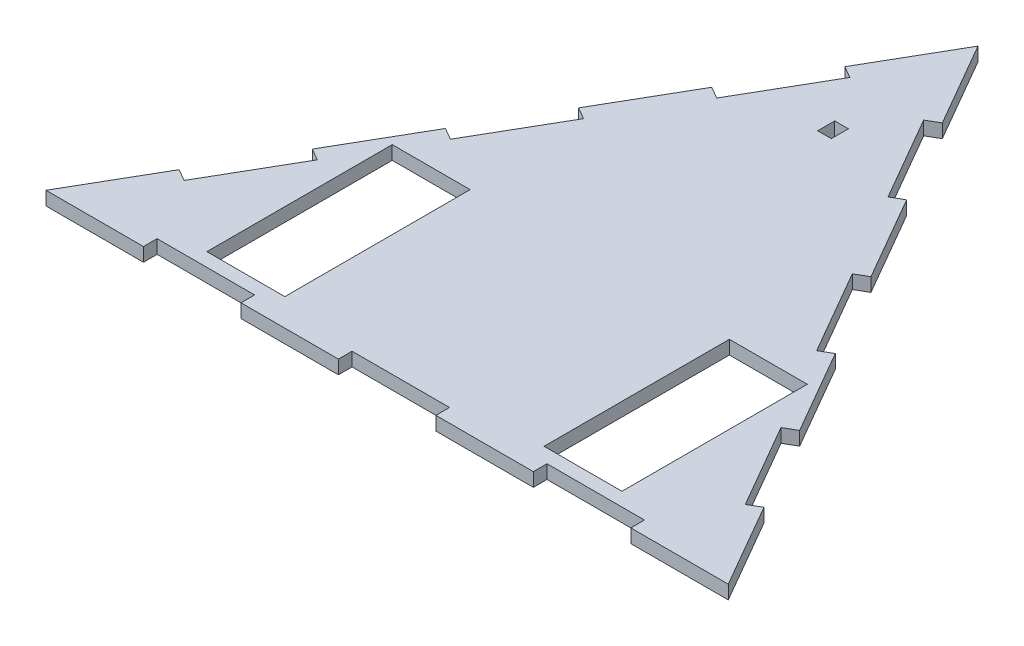
SolidWorks part; units mm, degrees
ref_plane "Front Plane" through (0, 0, 0) normal (0, 0, 1) x (1, 0, 0)
ref_plane "Top Plane" through (0, 0, 0) normal (0, 1, 0) x (1, 0, 0)
ref_plane "Right Plane" through (0, 0, 0) normal (1, 0, 0) x (0, 0, -1)
sketch "Sketch1" plane through (0, 0, 0) normal (0, 1, 0) x (1, 0, 0)
  line L0 (0, 0) -> (-254, 0)
  line L1 (-254, 0) -> (-127, 219.9705)
  line L2 (-127, 219.9705) -> (0, 0)
  dimension "D1" = 254
  dimension "D2" = 254
  dimension "D3" = 254
extrude "Boss-Extrude1" add sketch "Sketch1" along normal blind 5.08
sketch "Sketch4" plane through (0, 5.08, 0) normal (0, 1, 0) x (1, 0, 0)
  line L0 (-127, 0) -> (-175.26, 0) construction
  line L1 (-254, 0) -> (0, 0) construction
  line L2 (-127, 0) -> (-78.74, 0) construction
  line L3 (-175.26, 0) -> (-175.26, 10.16)
  line L4 (-78.74, 0) -> (-78.74, 10.16)
  line L6 (-175.26, 10.16) -> (-204.26, 10.16)
  line L7 (-175.26, 10.16) -> (-175.26, 79.16)
  line L8 (-175.26, 79.16) -> (-204.26, 79.16)
  line L9 (-204.26, 10.16) -> (-204.26, 79.16)
  line L10 (-78.74, 10.16) -> (-49.74, 10.16)
  line L11 (-78.74, 10.16) -> (-78.74, 79.16)
  line L12 (-78.74, 79.16) -> (-49.74, 79.16)
  line L13 (-49.74, 10.16) -> (-49.74, 79.16)
  dimension "D1" = 48.26
  dimension "D2" = 48.26
  dimension "D3" = 10.16
  dimension "D4" = 10.16
  dimension "D5" = 69
  dimension "D6" = 29
  dimension "D7" = 69
  dimension "D8" = 29
extrude "Cut-Extrude1" cut sketch "Sketch4" against normal blind 5.08 contours L9 L6 L7 L8 | L10 L13 L12 L11
sketch "Sketch8" plane through (-190.5, 0, -109.9852) normal (-0.866, 0, -0.5) x (-0.5, 0, 0.866)
  line L0 (-127, 0) -> (-90.7143, 0) construction
  line L1 (-127, 0) -> (127, 0) construction
  line L2 (-90.7143, 0) -> (-54.4286, 0) construction
  line L3 (-54.4286, 0) -> (-18.1429, 0) construction
  line L4 (-18.1429, 0) -> (18.1429, 0) construction
  line L5 (18.1429, 0) -> (54.4286, 0) construction
  line L6 (54.4286, 0) -> (90.7143, 0) construction
  line L7 (90.7143, 0) -> (127, 0) construction
  line L8 (-127, 5.08) -> (127, 5.08) construction
  line L9 (-90.7143, 0) -> (-54.4286, 0)
  line L10 (-90.7143, 0) -> (-90.7143, 5.08)
  line L11 (-90.7143, 5.08) -> (-54.4286, 5.08)
  line L12 (-54.4286, 0) -> (-54.4286, 5.08)
  line L14 (-18.1429, 0) -> (18.1429, 0)
  line L15 (-18.1429, 0) -> (-18.1429, 5.08)
  line L16 (-18.1429, 5.08) -> (18.1429, 5.08)
  line L17 (18.1429, 0) -> (18.1429, 5.08)
  line L18 (54.4286, 0) -> (90.7143, 0)
  line L19 (54.4286, 0) -> (54.4286, 5.08)
  line L20 (54.4286, 5.08) -> (90.7143, 5.08)
  line L21 (90.7143, 0) -> (90.7143, 5.08)
extrude "Cut-Extrude2" cut sketch "Sketch8" against normal blind 5.08
sketch "Sketch9" plane through (0, 0, 0) normal (0, 0, 1) x (1, 0, 0)
  line L0 (0, 0) -> (-36.2857, 0) construction
  line L1 (-254, 0) -> (0, 0) construction
  line L2 (-36.2857, 0) -> (-72.5714, 0) construction
  line L3 (-72.5714, 0) -> (-108.8571, 0) construction
  line L4 (-108.8571, 0) -> (-145.1429, 0) construction
  line L5 (-145.1429, 0) -> (-181.4286, 0) construction
  line L6 (-181.4286, 0) -> (-217.7143, 0) construction
  line L7 (-217.7143, 0) -> (-254, 0) construction
  line L8 (-254, 5.08) -> (0, 5.08) construction
  line L9 (-36.2857, 0) -> (-72.5714, 0)
  line L10 (-36.2857, 0) -> (-36.2857, 5.08)
  line L11 (-36.2857, 5.08) -> (-72.5714, 5.08)
  line L12 (-72.5714, 0) -> (-72.5714, 5.08)
  line L14 (-108.8571, 0) -> (-145.1429, 0)
  line L15 (-108.8571, 0) -> (-108.8571, 5.08)
  line L16 (-108.8571, 5.08) -> (-145.1429, 5.08)
  line L17 (-145.1429, 0) -> (-145.1429, 5.08)
  line L18 (-181.4286, 0) -> (-217.7143, 0)
  line L19 (-181.4286, 0) -> (-181.4286, 5.08)
  line L20 (-181.4286, 5.08) -> (-217.7143, 5.08)
  line L21 (-217.7143, 0) -> (-217.7143, 5.08)
extrude "Cut-Extrude3" cut sketch "Sketch9" against normal blind 5.08
sketch "Sketch10" plane through (0, 0, 0) normal (0.866, 0, -0.5) x (-0.5, 0, -0.866)
  line L0 (0, 0) -> (36.2857, 0) construction
  line L1 (0, 0) -> (254, 0) construction
  line L2 (36.2857, 0) -> (72.5714, 0) construction
  line L3 (72.5714, 0) -> (108.8571, 0) construction
  line L4 (108.8571, 0) -> (145.1429, 0) construction
  line L5 (145.1429, 0) -> (181.4286, 0) construction
  line L6 (181.4286, 0) -> (217.7143, 0) construction
  line L7 (217.7143, 0) -> (254, 0) construction
  line L8 (0, 5.08) -> (254, 5.08) construction
  line L9 (36.2857, 0) -> (72.5714, 0)
  line L10 (36.2857, 0) -> (36.2857, 5.08)
  line L11 (36.2857, 5.08) -> (72.5714, 5.08)
  line L12 (72.5714, 0) -> (72.5714, 5.08)
  line L14 (108.8571, 0) -> (145.1429, 0)
  line L15 (108.8571, 0) -> (108.8571, 5.08)
  line L16 (108.8571, 5.08) -> (145.1429, 5.08)
  line L17 (145.1429, 0) -> (145.1429, 5.08)
  line L18 (181.4286, 0) -> (217.7143, 0)
  line L19 (181.4286, 0) -> (181.4286, 5.08)
  line L20 (181.4286, 5.08) -> (217.7143, 5.08)
  line L21 (217.7143, 0) -> (217.7143, 5.08)
extrude "Cut-Extrude4" cut sketch "Sketch10" against normal blind 5.08
sketch "Sketch12" plane through (0, 5.08, 0) normal (0, 1, 0) x (1, 0, 0)
  line L0 (-127, 219.9705) -> (-127, 169.1705) construction
  line L1 (-133.772, 5.08) -> (-145.1429, 5.08)
  line L2 (-108.8571, 5.08) -> (-145.1429, 5.08) construction
  line L3 (-145.1429, 5.08) -> (-145.1429, 169.1705) construction
  line L6 (-108.8571, 169.1705) -> (-108.8571, 5.08) construction
  line L7 (-108.8571, 5.08) -> (-145.1429, 5.08) construction
  line L8 (-145.1429, 169.1705) -> (-129.54, 169.1705) construction
  line L9 (-129.54, 169.1705) -> (-124.46, 169.1705) construction
  line L10 (-124.46, 169.1705) -> (-108.8571, 169.1705) construction
  line L12 (-129.54, 169.1705) -> (-124.46, 169.1705)
  line L13 (-129.54, 169.1705) -> (-129.54, 162.8205)
  line L14 (-129.54, 162.8205) -> (-124.46, 162.8205)
  line L15 (-124.46, 169.1705) -> (-124.46, 162.8205)
  dimension "D1" = 50.8
  dimension "D2" = 5.08
  dimension "D3" = 6.35
extrude "Cut-Extrude6" cut sketch "Sketch12" against normal blind 5.08 contours L15 L12 L13 L14
equation "\"MDFThickness\"= .2in"
equation "\"D1@Boss-Extrude1\"=\"MDFThickness\""
equation "\"D6@Sketch4\"=\"WheelThickness\" + 5mm"
equation "\"D8@Sketch4\"=\"WheelThickness\" + 5mm"
equation "\"D1@Cut-Extrude1\"=\"MDFThickness\""
equation "\"D3@Sketch4\"=\"MDFThickness\" * 2"
equation "\"D4@Sketch4\"=\"MDFThickness\" * 2"
equation "\"D1@Cut-Extrude2\"=\"MDFThickness\""
equation "\"D1@Cut-Extrude3\"=\"MDFThickness\""
equation "\"D1@Cut-Extrude4\"=\"MDFThickness\""
equation "\"D2@Sketch12\"=\"MDFThickness\""
equation "\"D1@Cut-Extrude6\"=\"MDFThickness\""
equation "\"WheelThickness\"= 24mm"
